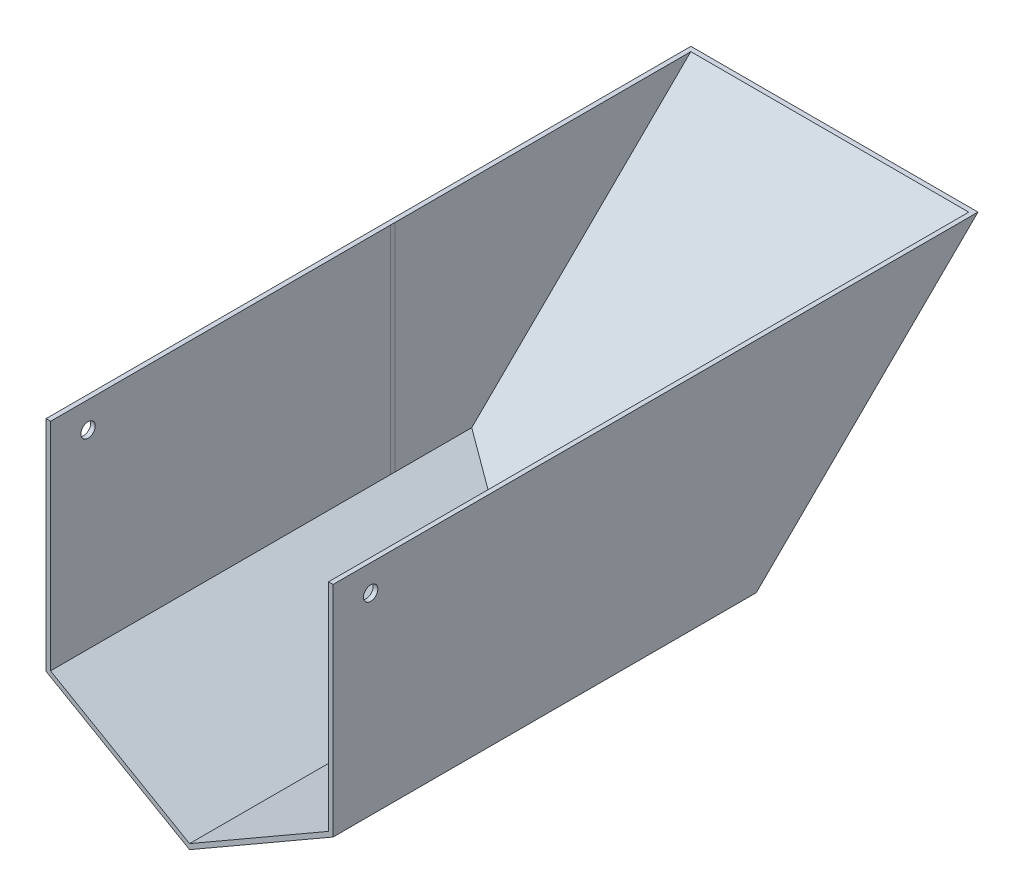
SolidWorks part; units mm, degrees
material "ABS"
ref_plane "Front Plane" through (0, 0, 0) normal (0, 0, 1) x (1, 0, 0)
ref_plane "Top Plane" through (0, 0, 0) normal (0, 1, 0) x (1, 0, 0)
ref_plane "Right Plane" through (0, 0, 0) normal (1, 0, 0) x (0, 0, -1)
sketch "Sketch1" plane through (0, 0, 0) normal (0, 1, 0) x (1, 0, 0)
  line L0 (1.5875, -1.5875) -> (98.4125, -1.5875)
  line L1 (0, 0) -> (100, 0)
  line L2 (0, 0) -> (0, -120)
  line L3 (0, -120) -> (1.5875, -120)
  line L4 (100, 0) -> (100, -120)
  line L5 (98.4125, -1.5875) -> (98.4125, -118.4125)
  line L7 (1.5875, -1.5875) -> (1.5875, -118.4125)
  line L8 (1.5875, -118.4125) -> (1.5875, -120)
  line L9 (98.4125, -118.4125) -> (98.4125, -120)
  line L10 (98.4125, -120) -> (100, -120)
  line L11 (1.5875, -118.4125) -> (98.4125, -118.4125) construction
  line L12 (0, -120) -> (100, -120) construction
  dimension "D1" = 100
  dimension "D2" = 120
  dimension "D3" = 1.5875
extrude "Boss-Extrude2" add sketch "Sketch1" along normal blind 76.2 contours L7 L8 L3 L2 L1 L4 L10 L9 L5 L0
sketch "Sketch2" plane through (0, 0, 120) normal (0, 0, 1) x (1, 0, 0)
  line L0 (0, 0) -> (1.5875, 0.9174)
  line L1 (100, 0) -> (98.4125, 0.9174)
  line L2 (50, -26.9816) -> (94.0658, -1.5875)
  line L3 (0, 0) -> (50, -28.8139)
  line L4 (50, -28.8139) -> (100, 0)
  line L5 (5.9342, -1.5875) -> (50, -26.9816)
  line L7 (50, -26.9816) -> (1.5875, 0.9174)
  line L8 (1.5875, 76.2) -> (1.5875, 0) construction
  line L9 (50, -26.9816) -> (98.4125, 0.9174)
  line L10 (98.4125, 76.2) -> (98.4125, 0) construction
  line L11 (0, 0) -> (100, 0) construction
  line L12 (5.9342, -1.5875) -> (94.0658, -1.5875) construction
  dimension "D1" = 1.5875
extrude "Boss-Extrude3" add sketch "Sketch2" against normal up to surface (118.4125 mm away) contours L7 L0 L3 L4 L1 L9 up to face at (50, 38.1, 1.5875)
sketch "Sketch3" plane through (98.4125, 0, 0) normal (-1, 0, 0) x (0, 0, 1)
  line L0 (1.5875, 0.9174) -> (-19.9785, 26.6187)
  line L1 (1.5875, 76.2) -> (1.5875, 0.9174) construction
  line L2 (1.5875, 0.9174) -> (1.5875, 76.2)
  line L3 (-19.9785, 26.6187) -> (-61.5821, 76.2)
  line L4 (-61.5821, 76.2) -> (1.5875, 76.2)
  dimension "D1" = 40
  dimension "D2" = 40
sketch "Sketch5" plane through (0, 76.2, 0) normal (0, 1, 0) x (1, 0, 0)
  line L0 (0, 0) -> (100, 0) construction
  line L1 (98.4125, -1.5875) -> (1.5873, -1.5875)
  line L2 (98.4125, -1.5875) -> (98.4125, 0)
  line L3 (98.4125, 0) -> (1.5873, 0)
  line L4 (1.5873, -1.5875) -> (1.5873, 0)
extrude "Cut-Extrude2" cut sketch "Sketch5" against normal up to surface (76.2 mm away) up to face at (50, 0, 1.0583)
sketch "Sketch10" plane through (0, 0, 0) normal (0, -1, 0) x (1, 0, 0)
  line L0 (50, 1.5875) -> (50, 120) construction
  line L1 (50, 1.5875) -> (50, 120)
  line L2 (50, 1.5875) -> (50, -30.4172)
  line L3 (98.4125, 1.5875) -> (98.4125, -27.3387)
  line L4 (98.4125, -27.3387) -> (0, -27.3387)
  line L5 (100, 1.5875) -> (100, -27.3387)
  line L6 (0, -27.3387) -> (0, 1.5875)
  line L7 (98.4125, 1.5875) -> (100, 0)
  line L8 (1.5873, 1.5875) -> (1.5873, -27.3387)
  line L9 (100, 0) -> (100, 1.5875)
  line L10 (100, 1.5875) -> (98.4125, 1.5875)
  line L11 (1.5873, 1.5875) -> (0, 1.5875)
  line L12 (0, 1.5875) -> (0, 0)
  line L13 (100, -27.3387) -> (98.4125, -27.3387)
  line L14 (100, -25.7512) -> (0, -25.7512)
  dimension "D1" = 1.5875
ref_plane "Plane2" through (50, 0, 0) normal (-1, 0, 0) x (0, 0, 1)
sketch "Sketch11" plane through (50, 0, 0) normal (-1, 0, 0) x (0, 0, 1)
  line L0 (1.5875, -26.9816) -> (-25.7614, 0)
  line L1 (1.5875, 0) -> (-30.4172, 0) construction
  line L2 (-25.7614, 0) -> (-27.3845, 0)
  line L3 (-27.3845, 0) -> (1.5875, -28.8139)
  line L4 (-25.1381, -0.6149) -> (-117.8141, 90.8163)
  line L5 (-27.3845, 0) -> (-118.6146, 90.0049)
  line L6 (-118.6146, 90.0049) -> (-117.8141, 90.8163)
  line L7 (-117.8141, 90.8163) -> (-117.8756, 91.1728)
  line L8 (1.5875, -26.9816) -> (1.5875, -28.8139)
extrude "Boss-Extrude5" add sketch "Sketch11" along normal up to surface and the other way up to surface contours L8 L0 L2 L3 | L6 L5 L2 L4 up to face at (0, 30.48, 48.3175) other way up to face at (100, 30.48, 48.3175)
sketch "Sketch12" plane through (0, 0, 1.5875) normal (0, 0, -1) x (-1, 0, 0)
  line L0 (-98.4125, 0.9174) -> (-100, 0)
  line L1 (-100, 0) -> (-98.4125, 0.9174)
  line L2 (-98.4125, 0.9174) -> (-100, 0.9174)
  line L3 (-50, -26.9816) -> (-98.4125, 0.9174) construction
  line L4 (-100, 0) -> (-100, 0.9174)
  line L5 (-100, 0.9174) -> (-98.4125, 0.9174)
  line L6 (-100, 0) -> (-98.4125, 0)
  line L7 (-98.4125, 0) -> (-98.4125, 0.9174)
  line L8 (-53.1794, -26.9816) -> (-100, 0) construction
  line L9 (-50, -26.9816) -> (-1.5875, 0.9174) construction
  line L10 (0, 0) -> (-46.8206, -26.9816) construction
  line L11 (-1.5873, 0) -> (0, 0) construction
  line L12 (-50, -26.9816) -> (-98.4125, 0.9174)
  line L13 (-53.1794, -26.9816) -> (-100, 0)
  line L14 (-50, -26.9816) -> (-1.5875, 0.9174)
  line L15 (0, 0) -> (-46.8206, -26.9816)
  line L16 (-1.5873, 0) -> (0, 0)
  line L17 (0, 0) -> (0, 0.9174)
  line L18 (0, 0.9174) -> (-1.5875, 0.9174)
  line L19 (-53.1794, -26.9816) -> (-50, -28.8139)
  line L20 (-50, -28.8139) -> (-46.8206, -26.9816)
extrude "Boss-Extrude6" add sketch "Sketch12" along normal up to surface (1.8423 mm away)
sketch "Sketch13" plane through (0, 0, 0) normal (-1, 0, 0) x (0, 0, 1)
  line L0 (0, 76.2) -> (-102.9988, 76.2)
  line L1 (-117.8141, 90.8163) -> (-26.6913, 0.9174) construction
  line L2 (-102.9988, 76.2) -> (-26.6913, 0.9174)
  line L3 (-26.6913, 0.9174) -> (0, 0.9174)
  line M4 (0, 76.2) -> (0, 0.9174)
  line M5 (0, 0.9174) -> (-26.6913, 0.9174)
  line M6 (-26.6913, 0.9174) -> (-117.8141, 90.8163)
extrude "Boss-Extrude7" add sketch "Sketch13" against normal blind 1.5875 contours L0 M4 M6 M5
sketch "Sketch14" plane through (100, 0, 0) normal (1, 0, 0) x (0, 0, -1)
  line L0 (0, 0) -> (25.7614, 0)
  line L1 (0, 0) -> (0, 76.2)
  line L2 (0, 76.2) -> (102.9988, 76.2)
  line L3 (25.7614, 0) -> (117.8141, 90.8163) construction
  line L4 (102.9988, 76.2) -> (25.7614, 0)
extrude "Boss-Extrude8" add sketch "Sketch14" against normal blind 1.5875
sketch "Sketch15" plane through (0, 0, 120) normal (0, 0, 1) x (1, 0, 0)
  line L1 (100, 76.2) -> (-43.3263, 76.2)
  line L2 (100, 76.2) -> (100, 129.4557)
  line L3 (100, 129.4557) -> (-43.3263, 129.4557)
  line L4 (-43.3263, 76.2) -> (-43.3263, 129.4557)
extrude "Cut-Extrude3" cut sketch "Sketch15" against normal blind 264.5875
sketch "Sketch16" plane through (0, 0, 120) normal (0, 0, 1) x (1, 0, 0)
  line L0 (50, -28.8139) -> (-14.8918, -42.4729)
  line L1 (-14.8918, -42.4729) -> (-24.6317, 0)
  line L2 (-24.6317, 0) -> (0, 0)
  line L3 (0, 0) -> (50, -28.8139)
  line L4 (50, -28.8139) -> (100, 0)
  line L5 (100, 0) -> (131.4881, 0)
  line L6 (131.4881, 0) -> (150.5084, -66.0922)
  line L7 (150.5084, -66.0922) -> (63.7607, -52.6925)
  line L8 (63.7607, -52.6925) -> (50, -28.8139)
  line M5 (0, 0) -> (50, -28.8139)
  line M6 (50, -28.8139) -> (100, 0)
extrude "Cut-Extrude4" cut sketch "Sketch16" against normal blind 264.5875 contours L8 L7 L6 L5 M6 | L2 L1 L0 M5
sketch "Sketch18" plane through (0, 0, 0) normal (-1, 0, 0) x (0, 0, 1)
  circle A0 centre (106.931, 67.0396) radius 2.5
extrude "Cut-Extrude5" cut sketch "Sketch18" against normal blind 264.5875
